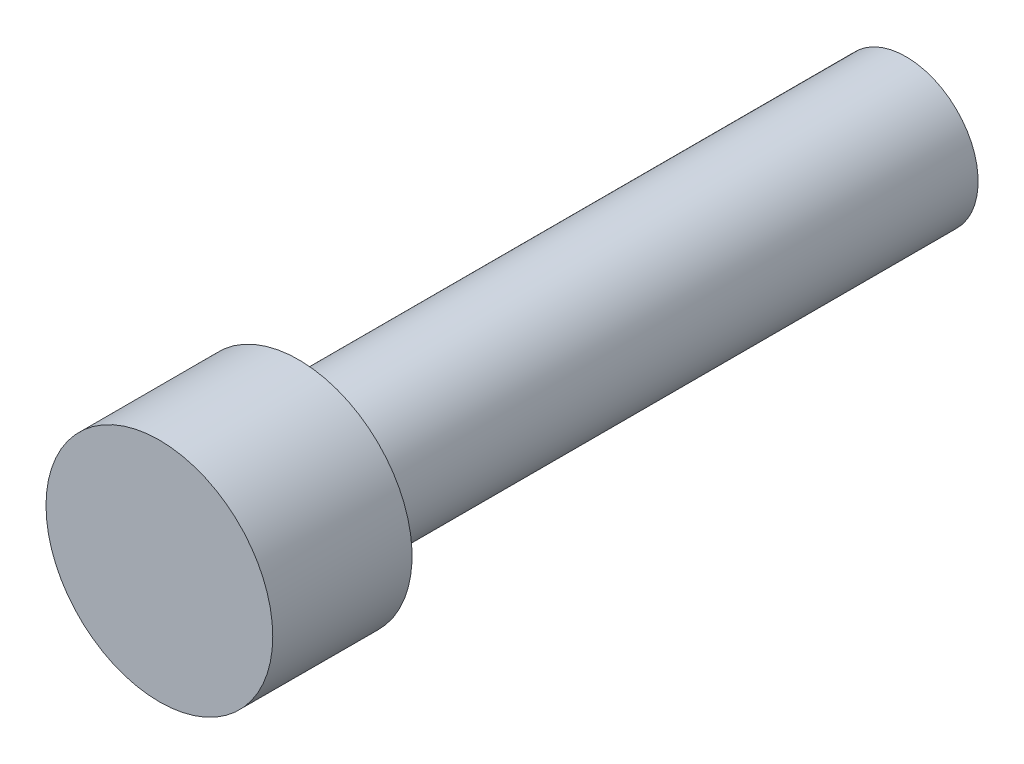
SolidWorks part; units mm, degrees
ref_plane "Front Plane" through (0, 0, 0) normal (0, 0, 1) x (1, 0, 0)
ref_plane "Top Plane" through (0, 0, 0) normal (0, 1, 0) x (1, 0, 0)
ref_plane "Right Plane" through (0, 0, 0) normal (1, 0, 0) x (0, 0, -1)
sketch "Sketch1" plane through (0, 0, 0) normal (0, 0, 1) x (1, 0, 0)
  circle A0 centre (0, 0) radius 1.778
extrude "Extrude1" add sketch "Sketch1" along normal blind 11.7094
sketch "Sketch3" plane through (0, 0, 0) normal (0, 0, -1) x (-1, 0, 0)
  circle A0 centre (0, 0) radius 1.1303
extrude "Extrude2" cut sketch "Sketch3" against normal blind 9.525 flip side to cut
